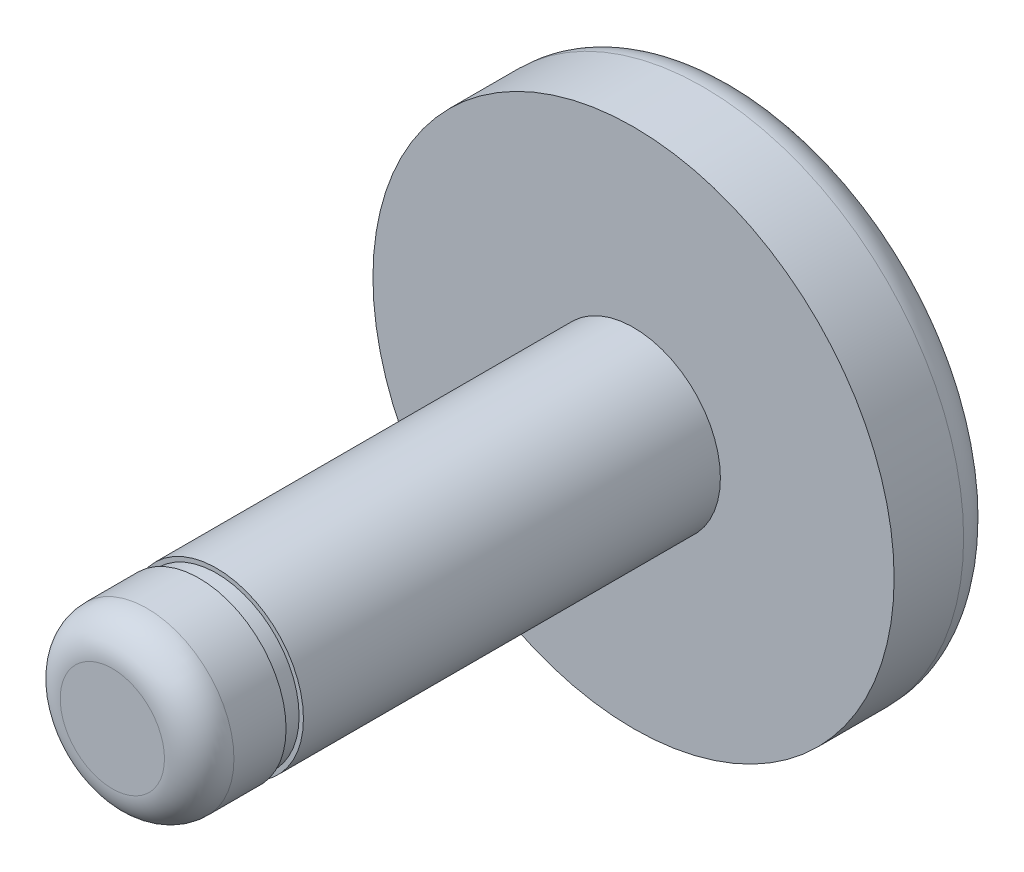
SolidWorks part; units mm, degrees
ref_plane "Front Plane" through (0, 0, 0) normal (0, 0, 1) x (1, 0, 0)
ref_plane "Top Plane" through (0, 0, 0) normal (0, 1, 0) x (1, 0, 0)
ref_plane "Right Plane" through (0, 0, 0) normal (1, 0, 0) x (0, 0, -1)
sketch "Sketch1" plane through (0, 0, 0) normal (0, 0, 1) x (1, 0, 0)
  circle A0 centre (0, 0) radius 7.5
  dimension "D1" = 15
extrude "Boss-Extrude1" add sketch "Sketch1" along normal blind 3
sketch "Sketch3" plane through (0, 0, 3) normal (0, 0, 1) x (1, 0, 0)
  circle A0 centre (0, 0) radius 2.5
  dimension "D1" = 5
extrude "Boss-Extrude3" add sketch "Sketch3" along normal blind 15
fillet "Fillet1" radius 1 2 edges at (7.5, 0, 0) (2.5, 0, 18)
ref_plane "Plane1" through (0, 0, 15) normal (0, 0, 1) x (1, 0, 0)
sketch "Sketch4" plane through (0, 0, 15) normal (0, 0, 1) x (1, 0, 0)
  circle A0 centre (0, 0) radius 2.375
  dimension "D1" = 4.75
extrude "Cut-Extrude-Thin1" cut sketch "Sketch4" along normal blind 0.5 thin
